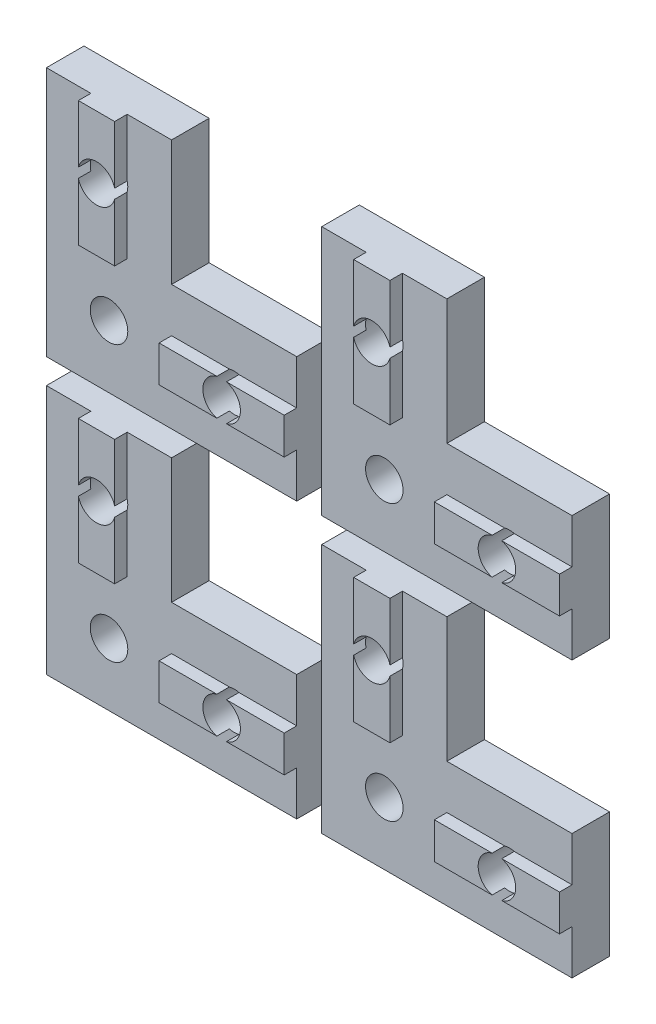
SolidWorks part; units mm, degrees
ref_plane "Front Plane" through (0, 0, 0) normal (0, 0, 1) x (1, 0, 0)
ref_plane "Top Plane" through (0, 0, 0) normal (0, 1, 0) x (1, 0, 0)
ref_plane "Right Plane" through (0, 0, 0) normal (1, 0, 0) x (0, 0, -1)
sketch "Esquisse1" plane through (0, 0, 0) normal (0, 0, 1) x (1, 0, 0)
  line L0 (0, 0) -> (20, 0)
  line L1 (20, 0) -> (20, 10)
  line L2 (20, 10) -> (10, 10)
  line L3 (10, 10) -> (10, 20)
  line L4 (10, 20) -> (0, 20)
  line L5 (0, 20) -> (0, 0)
  dimension "D1" = 10
  dimension "D3" = 20
extrude "Boss.-Extru.1" add sketch "Esquisse1" along normal blind 3
sketch "Esquisse2" plane through (0, 0, 3) normal (0, 0, 1) x (1, 0, 0)
  line L0 (10, 20) -> (0, 20) construction
  line L1 (3.55, 20) -> (6.45, 20)
  line L2 (3.55, 20) -> (3.55, 10)
  line L3 (3.55, 10) -> (6.45, 10)
  line L4 (6.45, 20) -> (6.45, 10)
  line L5 (20, 10) -> (10, 10) construction
  line L6 (20, 0) -> (20, 10) construction
  line L7 (20, 6.45) -> (10, 6.45)
  line L8 (20, 6.45) -> (20, 3.55)
  line L9 (20, 3.55) -> (10, 3.55)
  line L10 (10, 6.45) -> (10, 3.55)
  line L11 (10, 10) -> (10, 20) construction
  point P4 (5, 20)
  point P7 (5, 20)
  point P18 (20, 5)
  point P19 (20, 5)
  dimension "D1" = 2.9
extrude "Boss.-Extru.2" add sketch "Esquisse2" along normal blind 1
sketch "Esquisse4" plane through (0, 0, 4) normal (0, 0, 1) x (1, 0, 0)
  line L0 (10, 20) -> (0, 20) construction
  line L1 (20, 0) -> (20, 10) construction
  circle A0 centre (5, 15) radius 1.5
  circle A1 centre (5, 5) radius 1.5
  circle A2 centre (15, 5) radius 1.5
  point P9 (5, 20)
  point P12 (20, 5)
  dimension "D3" = 3
  dimension "D1" = 5
  dimension "D2" = 5
extrude "Enlèv. mat.-Extru.2" cut sketch "Esquisse4" against normal through all
pattern_linear "LPattern1" count 2 spacing 22 along (1, 0, 0) count 2 spacing 22 along (0, -1, 0) of bodies 104
